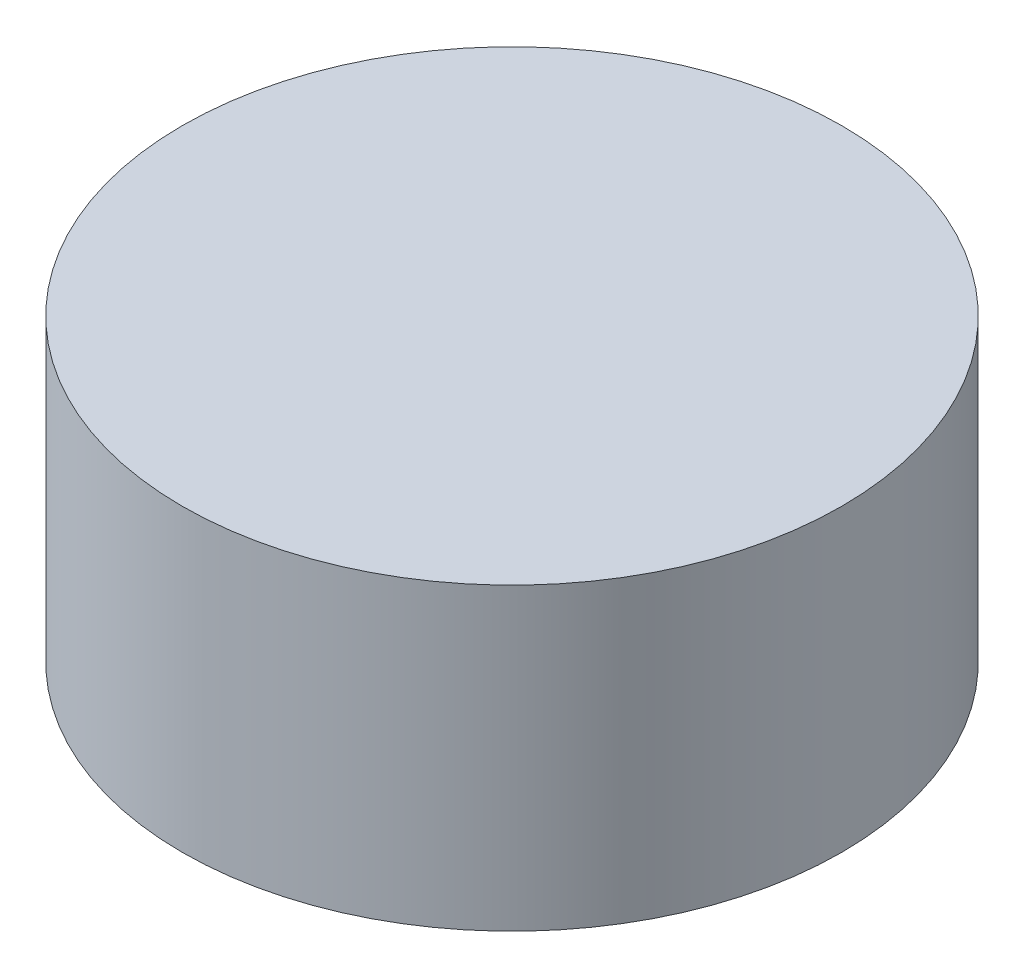
SolidWorks part; units mm, degrees
ref_plane "前基準面" through (0, 0, 0) normal (0, 0, 1) x (1, 0, 0)
ref_plane "上基準面" through (0, 0, 0) normal (0, 1, 0) x (1, 0, 0)
ref_plane "右基準面" through (0, 0, 0) normal (1, 0, 0) x (0, 0, -1)
sketch "草圖2" plane through (0, 0, 0) normal (0, 1, 0) x (1, 0, 0)
  circle A0 centre (0, 0) radius 5.5
  dimension "D1" = 11
extrude "填料-伸長1" add sketch "草圖2" along normal blind 5
